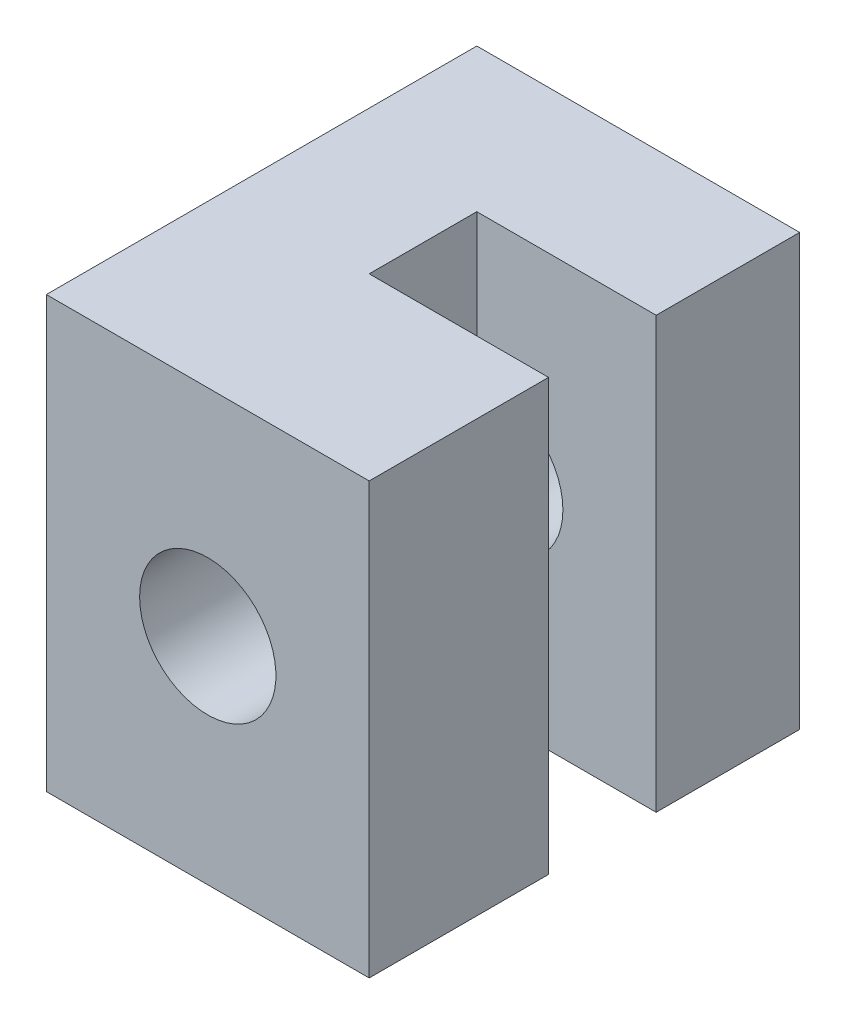
SolidWorks part; units mm, degrees
ref_plane "Front Plane" through (0, 0, 0) normal (0, 0, 1) x (1, 0, 0)
ref_plane "Top Plane" through (0, 0, 0) normal (0, 1, 0) x (1, 0, 0)
ref_plane "Right Plane" through (0, 0, 0) normal (1, 0, 0) x (0, 0, -1)
sketch "Sketch1" plane through (0, 0, 0) normal (0, 1, 0) x (1, 0, 0)
  line L1 (-4.5, -6) -> (4.5, -6)
  line L2 (-4.5, -6) -> (-4.5, 6)
  line L3 (-4.5, 6) -> (4.5, 6)
  line L4 (4.5, -6) -> (4.5, 6)
  line L5 (-4.5, -6) -> (4.5, 6) construction
  line L6 (-4.5, 6) -> (4.5, -6) construction
  line L7 (4.5, -6) -> (-0.5, -6)
  line L8 (4.5, -6) -> (4.5, -1)
  line L9 (4.5, -1) -> (-0.5, -1)
  line L10 (-0.5, -6) -> (-0.5, -1)
  line L11 (-0.5, -1) -> (4.5, -1)
  line L12 (-0.5, -1) -> (-0.5, 2)
  line L13 (-0.5, 2) -> (4.5, 2)
  line L14 (4.5, -1) -> (4.5, 2)
  point P0 (0, 0)
  point P11 (0, 0)
  dimension "D1" = 4
  dimension "D2" = 12
  dimension "D3" = 5
  dimension "D4" = 3
  dimension "D5" = 5
extrude "Boss-Extrude2" add sketch "Sketch1" along normal mid plane 12 contours L12 L13 L4 L3 L2 L1 L10 | L10 L1 L4 L9
sketch "Sketch2" plane through (0, 0, -6) normal (0, 0, -1) x (-1, 0, 0)
  line L1 (-7, -6) -> (7, -6) construction
  line L2 (-7, -6) -> (-7, 6) construction
  line L3 (-7, 6) -> (7, 6) construction
  line L4 (7, -6) -> (7, 6) construction
  line L5 (-7, -6) -> (7, 6) construction
  line L6 (-7, 6) -> (7, -6) construction
  line L9 (0, 0) -> (0, 6) construction
  line L10 (0, 6) -> (-2, 6) construction
  line L11 (-2, 6) -> (-7, 6) construction
  line L12 (0.5, 6) -> (0.5, -6) construction
  circle A0 centre (0, 0) radius 1.9
  point P0 (0, 0)
  point P13 (0, 0)
  dimension "D1" = 3.8
  dimension "D3" = 2
extrude "Cut-Extrude1" cut sketch "Sketch2" against normal through all contours A0
